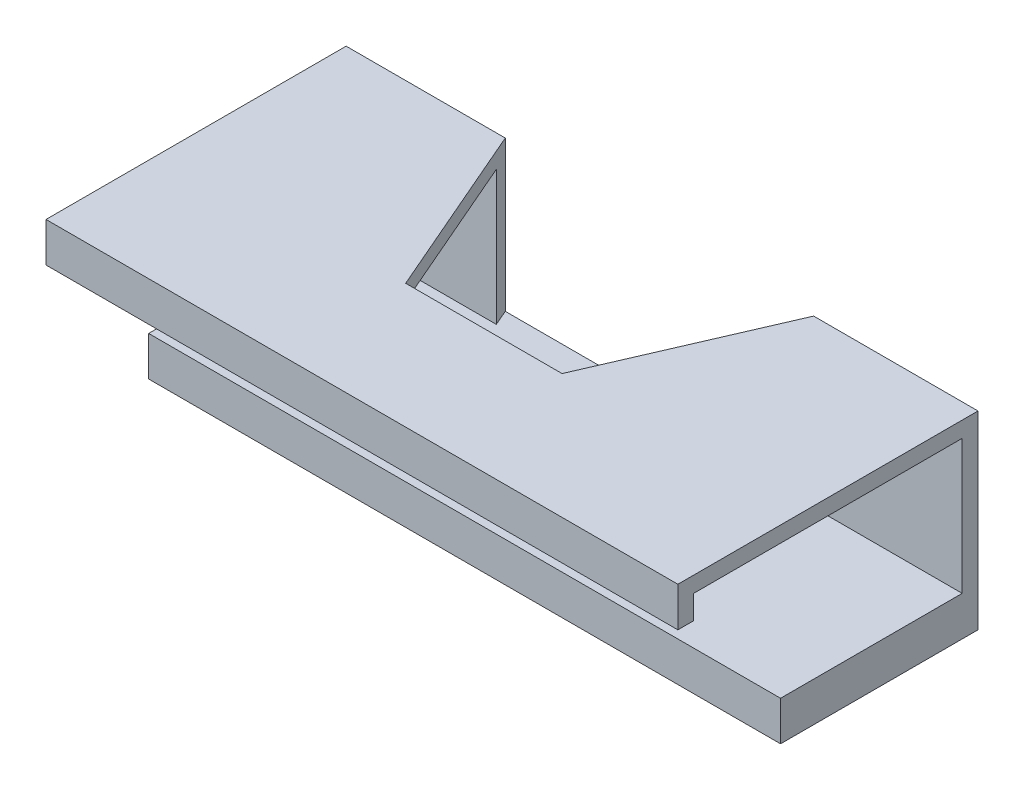
SolidWorks part; units mm, degrees
ref_plane "Front Plane" through (0, 0, 0) normal (0, 0, 1) x (1, 0, 0)
ref_plane "Top Plane" through (0, 0, 0) normal (0, 1, 0) x (1, 0, 0)
ref_plane "Right Plane" through (0, 0, 0) normal (1, 0, 0) x (0, 0, -1)
sketch "Sketch1" plane through (0, 0, 0) normal (0, 1, 0) x (1, 0, 0)
  line L1 (0, 0) -> (80, 0)
  line L2 (0, 0) -> (0, 25)
  line L3 (0, 25) -> (80, 25)
  line L4 (80, 0) -> (80, 25)
  dimension "D1" = 80
  dimension "D2" = 25
extrude "Boss-Extrude1" add sketch "Sketch1" along normal blind 5
sketch "Sketch2" plane through (0, 0, 0) normal (-1, 0, 0) x (0, 0, 1)
  line L0 (-25, 5) -> (-25, 24)
  line L1 (-25, 24) -> (13, 24)
  line L2 (13, 24) -> (13, 19)
  line L3 (13, 19) -> (11, 19)
  line L4 (11, 19) -> (11, 22)
  line L5 (11, 22) -> (-23, 22)
  line L6 (-23, 22) -> (-23, 5)
  line L7 (-25, 5) -> (0, 5) construction
  line L8 (-23, 5) -> (-25, 5)
  dimension "D1" = 2
  dimension "D2" = 2
  dimension "D3" = 34
  dimension "D4" = 2
  dimension "D5" = 3
  dimension "D6" = 17
extrude "Boss-Extrude2" add sketch "Sketch2" against normal blind 80
sketch "Sketch3" plane through (0, 24, 0) normal (0, 1, 0) x (1, 0, 0)
  line L0 (59.1907, 25) -> (49.5693, 2.7684)
  line L1 (80, 25) -> (0, 25) construction
  line L2 (49.5693, 2.7684) -> (29.7698, 2.7684)
  line L3 (29.7698, 2.7684) -> (20.1484, 25)
  line L4 (20.1484, 25) -> (59.1907, 25)
  point P5 (39.6696, 2.7684)
  point P7 (39.6696, 25)
extrude "Cut-Extrude1" cut sketch "Sketch3" against normal up to surface (19 mm away) up to face at (40, 5, -11.5)
